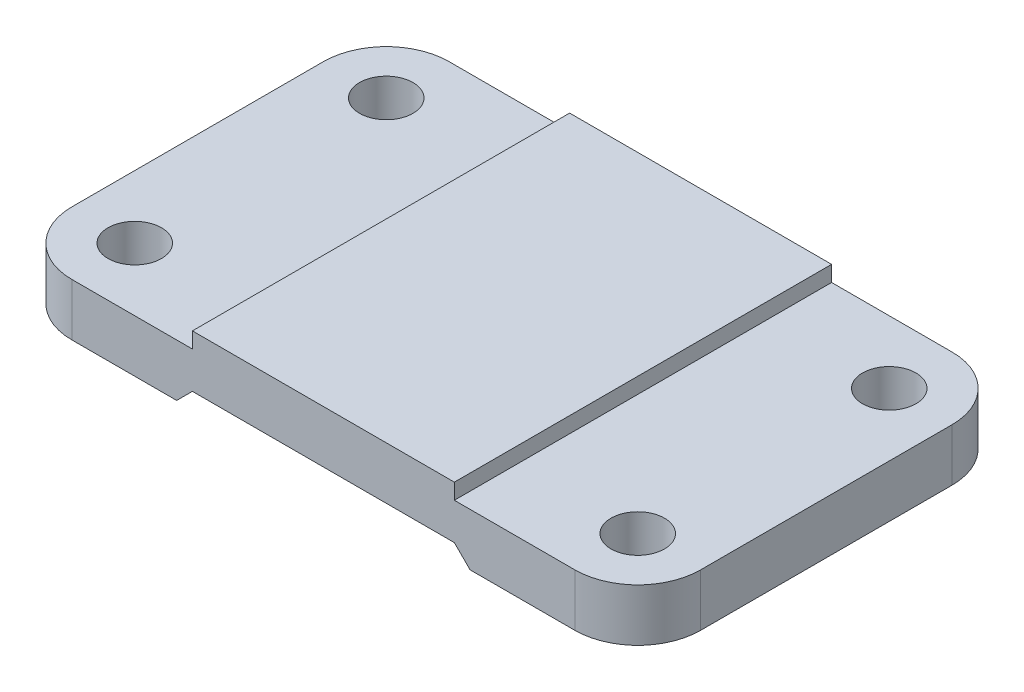
SolidWorks part; units mm, degrees
ref_plane "Front Plane" through (0, 0, 0) normal (0, 0, 1) x (1, 0, 0)
ref_plane "Top Plane" through (0, 0, 0) normal (0, 1, 0) x (1, 0, 0)
ref_plane "Right Plane" through (0, 0, 0) normal (1, 0, 0) x (0, 0, -1)
sketch "Sketch1" plane through (0, 0, 0) normal (0, 1, 0) x (1, 0, 0)
  line L0 (12, 0) -> (108, 0)
  line L1 (0, 12) -> (0, 60)
  line L2 (12, 72) -> (108, 72)
  line L3 (120, 60) -> (120, 12)
  line L4 (85, 72) -> (85, 0)
  line L5 (35, 0) -> (35, 72)
  arc A0 (108, 0) -> (120, 12) centre (108, 12) ccw
  arc A1 (12, 0) -> (0, 12) centre (12, 12) cw
  arc A2 (0, 60) -> (12, 72) centre (12, 60) cw
  arc A3 (108, 72) -> (120, 60) centre (108, 60) cw
  circle A4 centre (12, 60) radius 5.1
  circle A5 centre (12, 12) radius 5.1
  circle A6 centre (108, 60) radius 5.1
  circle A7 centre (108, 12) radius 5.1
  point P9 (0, 0)
  dimension "D1" = 12
  dimension "D2" = 12
  dimension "D3" = 50
extrude "Boss-Extrude7" add sketch "Sketch1" along normal blind 10 contours A2 L1 A1 L0 L5 L2 A5 A4 | L5 L0 L4 L2 | A3 L2 L4 L0 A0 L3 A7 A6
sketch "Sketch5" plane through (0, 0, 0) normal (0, 0, 1) x (1, 0, 0)
  line L0 (32, 0) -> (35, 3)
  line L1 (35, 3) -> (85, 3)
  line L2 (12, 0) -> (108, 0) construction
  line L3 (85, 3) -> (88, 0)
  line L8 (12, 0) -> (108, 0)
  line L9 (108, 0) -> (108, 10)
  line L10 (108, 10) -> (12, 10)
  line L11 (12, 10) -> (12, 0)
  line L12 (32, 0) -> (88, 0)
  dimension "D1" = 3
  dimension "D2" = 3
  dimension "D3" = 50
  dimension "D4" = 0
extrude "Cut-Extrude2" cut sketch "Sketch5" against normal blind 72
sketch "Sketch7" plane through (0, 10, 0) normal (0, 1, 0) x (1, 0, 0)
  line L0 (35, 72) -> (35, 0)
  line L1 (12, 72) -> (108, 72) construction
  line L2 (12, 0) -> (108, 0) construction
  line L3 (85, 72) -> (85, 0)
  line L4 (35, 72) -> (85, 72)
  line L5 (35, 0) -> (85, 0)
extrude "Boss-Extrude8" add sketch "Sketch7" along normal blind 3
